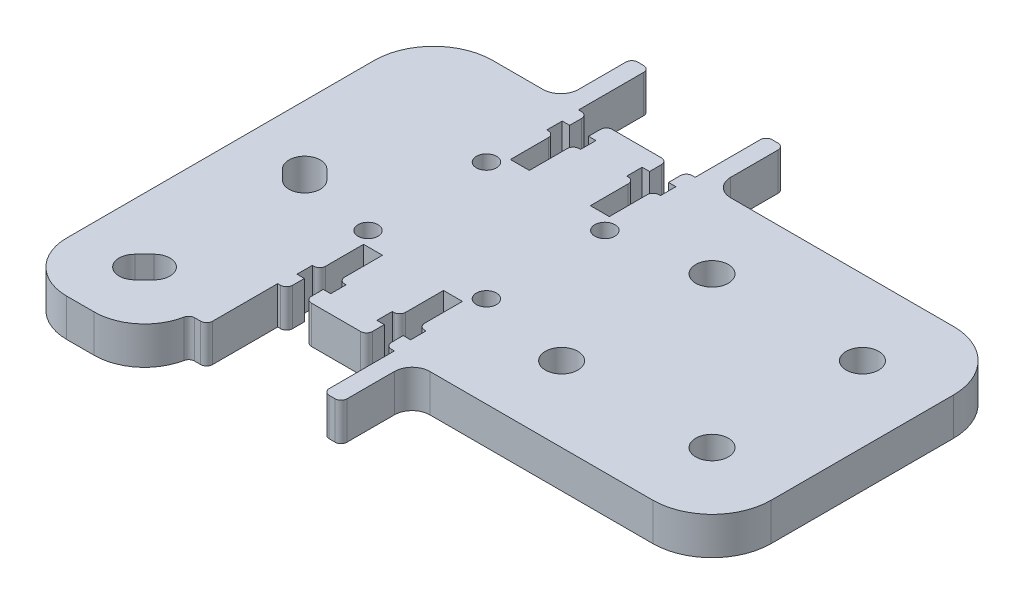
SolidWorks part; units mm, degrees
material "6061-T6 (SS)"
ref_plane "Front" through (0, 0, 0) normal (0, 0, 1) x (1, 0, 0)
ref_plane "Top" through (0, 0, 0) normal (0, 1, 0) x (1, 0, 0)
ref_plane "Right" through (0, 0, 0) normal (1, 0, 0) x (0, 0, -1)
sketch "Sketch1" plane through (0, 0, 0) normal (0, 1, 0) x (1, 0, 0)
  line L0 (-12.7, 25.4) -> (-12.7, -25.4) construction
  line L1 (38.1, -25.4) -> (-38.1, -25.4)
  line L2 (38.1, -25.4) -> (38.1, 25.4)
  line L3 (38.1, 25.4) -> (-38.1, 25.4)
  line L4 (-38.1, -25.4) -> (-38.1, 25.4) construction
  line L5 (38.1, -25.4) -> (-38.1, 25.4) construction
  line L6 (38.1, 25.4) -> (-38.1, -25.4) construction
  line L7 (25.4, -25.4) -> (25.4, 25.4) construction
  line L8 (0, 25.4) -> (0, -25.4) construction
  line L9 (38.1, 0) -> (-38.1, 0) construction
  line L10 (-12.7, 0) -> (-38.1, 0) construction
  line L11 (0, 0) -> (0, 25.4) construction
  line L12 (0, 12.7) -> (38.1, 12.7) construction
  line L13 (-25.4, 0) -> (-25.4, 25.4) construction
  line L14 (-15.4, 10) -> (-35.4, 10) construction
  line L15 (-38.1, 25.4) -> (-59.74, 25.4)
  line L16 (-59.74, 25.4) -> (-59.74, -45.04)
  line L17 (-59.74, -45.04) -> (-38.1, -45.04)
  line L18 (-38.1, -45.04) -> (-38.1, -25.4)
  line L19 (-38.1, 0) -> (-49.74, 0) construction
  line L20 (-49.74, -41.4) -> (-2.5231, -41.4) construction
  line L21 (-49.74, -35.04) -> (-49.74, -45.04) construction
  line L22 (-49.74, -6.36) -> (-49.74, -35.04) construction
  line L23 (-49.74, -6.36) -> (-59.74, -6.36) construction
  line L24 (-49.74, -6.36) -> (-49.74, -8.86) construction
  line L25 (-56.1, -6.36) -> (-56.1, -8) construction
  line L26 (-49.74, -6.36) -> (-48.1, -8) construction
  line L27 (-56.1, -6.36) -> (-56.1, -35.04) construction
  line L28 (-49.74, -35.04) -> (-48.1, -33.4) construction
  line L29 (-15.4, 12.5) -> (-35.4, 12.5) construction
  line L30 (-35.4, 12.5) -> (-35.4, 10) construction
  circle A0 centre (-15.4, 10) radius 1.5 construction
  circle A1 centre (-35.4, 10) radius 1.5 construction
  circle A2 centre (-35.4, -10) radius 1.5 construction
  circle A3 centre (-15.4, -10) radius 1.5 construction
  circle A4 centre (0, 12.7) radius 2.5 construction
  circle A5 centre (25.4, 12.7) radius 2.5 construction
  circle A6 centre (25.4, -12.7) radius 2.5 construction
  circle A7 centre (0, -12.7) radius 2.5 construction
  circle A8 centre (-49.74, -6.36) radius 6.36 construction
  circle A9 centre (-49.74, -35.04) radius 6.36 construction
  circle A10 centre (-49.74, -6.36) radius 10 construction
  circle A11 centre (-49.74, -35.04) radius 10 construction
  circle A12 centre (-49.74, -6.36) radius 2.5 construction
  circle A13 centre (-49.74, -35.04) radius 2.5 construction
  circle A14 centre (-48.1, -8) radius 8 construction
  circle A15 centre (-48.1, -8) radius 10 construction
  circle A16 centre (-48.1, -33.4) radius 8 construction
  point P0 (0, 0)
  point P23 (-25.4, 10)
  point P64 (-25.4, 12.5)
  dimension "D8" = 3
  dimension "D9" = 5
  dimension "D10" = 12.72
  dimension "D11" = 5
  dimension "D12" = 20
  dimension "D14" = 16
  dimension "D15" = 12.5
  dimension "D1" = 50.8
  dimension "D2" = 76.2
  dimension "D3" = 12.7
  dimension "D4" = 25.4
  dimension "D5" = 25.4
  dimension "D6" = 10
  dimension "D7" = 20
  dimension "D13" = 16
extrude "Boss-Extrude1" add sketch "Sketch1" along normal blind 6.35
fillet "Fillet1" radius 8.5 2 edges at (-59.74, 3.175, 45.04) (-38.1, 3.175, 45.04)
fillet "Fillet2" radius 10 3 edges at (38.1, 3.175, -25.4) (38.1, 3.175, 25.4) (-59.74, 3.175, -25.4)
hole_wizard "M5 Clearance Hole1" positions "Sketch3" profile "Sketch2" hole size "M5" standard "ISO" end condition through all
sketch "Sketch3" plane through (0, 6.35, 0) normal (0, 1, 0) x (-1, 0, 0)
  point P6 (0, 12.7)
  point P9 (-25.4, 12.7)
  point P12 (-25.4, -12.7)
  point P15 (0, -12.7)
sketch "Sketch2" plane through (0, 6.35, 12.7) normal (1, 0, 0) x (0, 0, 1)
  line L0 (0, 0) -> (0, 6.35)
  line L1 (0, 6.35) -> (2.75, 6.35)
  line L2 (2.75, 6.35) -> (2.75, 0)
  line L5 (2.75, 0) -> (0, 0)
  line L11 (0, -6.35) -> (0, 107.95) construction
  dimension "Thru Hole Dia." = 5.5
  dimension "Thru Hole Depth" = 6.35
hole_wizard "M3 Clearance Hole1" positions "Sketch5" profile "Sketch4" hole size "M3" standard "ISO" end condition through all
sketch "Sketch5" plane through (0, 6.35, 0) normal (0, 1, 0) x (-1, 0, 0)
  point P0 (15.4, 10)
  point P3 (15.4, -10)
  point P6 (35.4, -10)
  point P9 (35.4, 10)
sketch "Sketch4" plane through (-15.4, 6.35, 10) normal (1, 0, 0) x (0, 0, 1)
  line L0 (0, 0) -> (0, 6.35)
  line L1 (0, 6.35) -> (1.7, 6.35)
  line L2 (1.7, 6.35) -> (1.7, 0)
  line L5 (1.7, 0) -> (0, 0)
  line L11 (0, -6.35) -> (0, 107.95) construction
  dimension "Thru Hole Dia." = 3.4
  dimension "Thru Hole Depth" = 6.35
sketch "Sketch8" plane through (0, 6.35, 0) normal (0, 1, 0) x (1, 0, 0)
  line L0 (-49.74, -6.36) -> (-48.1, -8) construction
  line L1 (-51.6138, -8.2338) -> (-49.9738, -9.8738)
  line L2 (-47.8662, -4.4862) -> (-46.2262, -6.1262)
  line L3 (-49.74, -35.04) -> (-48.1, -33.4) construction
  line L4 (-47.8662, -36.9138) -> (-46.2262, -35.2738)
  line L5 (-51.6138, -33.1662) -> (-49.9738, -31.5262)
  arc A0 (-51.6138, -8.2338) -> (-47.8662, -4.4862) centre (-49.74, -6.36) cw
  arc A1 (-49.9738, -9.8738) -> (-46.2262, -6.1262) centre (-48.1, -8) ccw
  arc A2 (-47.8662, -36.9138) -> (-51.6138, -33.1662) centre (-49.74, -35.04) cw
  arc A3 (-46.2262, -35.2738) -> (-49.9738, -31.5262) centre (-48.1, -33.4) ccw
  dimension "D1" = 2.65
  dimension "D2" = 2.65
  dimension "D3" = 2.65
  dimension "D4" = 2.65
extrude "Cut-Extrude1" cut sketch "Sketch8" against normal through all
sketch "Sketch9" plane through (0, 6.35, 0) normal (0, 1, 0) x (1, 0, 0)
  line L0 (-25.4, 25.4) -> (-25.4, 0) construction
  line L1 (-15.55, 25.4) -> (-12.55, 25.4)
  line L2 (-15.55, 25.4) -> (-15.55, 37.4)
  line L3 (-15.55, 37.4) -> (-12.55, 37.4)
  line L4 (-12.55, 25.4) -> (-12.55, 37.4)
  line L5 (-38.25, 25.4) -> (-38.25, 37.4)
  line L6 (-35.25, 37.4) -> (-38.25, 37.4)
  line L7 (-35.25, 25.4) -> (-35.25, 37.4)
  line L8 (-35.25, 25.4) -> (-38.25, 25.4)
  line L9 (-38.1, 0) -> (0, 0) construction
  line L10 (38.1, 25.4) -> (-38.1, 25.4) construction
  line L11 (38.1, 0) -> (-38.1, 0) construction
  line L12 (-35.25, -25.4) -> (-38.25, -25.4)
  line L13 (-35.25, -25.4) -> (-35.25, -37.4)
  line L14 (-35.25, -37.4) -> (-38.25, -37.4)
  line L15 (-38.25, -25.4) -> (-38.25, -37.4)
  line L16 (-12.55, -25.4) -> (-12.55, -37.4)
  line L17 (-15.55, -37.4) -> (-12.55, -37.4)
  line L18 (-15.55, -25.4) -> (-15.55, -37.4)
  line L19 (-15.55, -25.4) -> (-12.55, -25.4)
  dimension "D1" = 12
  dimension "D2" = 3
  dimension "D3" = 19.7
extrude "Boss-Extrude2" add sketch "Sketch9" against normal up to surface (6.35 mm away) up to face at (-48.92, 0, 34.22)
sketch "Sketch10" plane through (0, 6.35, 0) normal (0, 1, 0) x (1, 0, 0)
  line L0 (-25.4, 25.4) -> (-25.4, -25.4) construction
  line L1 (-38.1, 0) -> (0, 0) construction
  line L2 (-32.15, 25.4) -> (-32.15, 12.4) construction
  line L3 (-33.75, 12.4) -> (-30.55, 12.4)
  line L4 (-30.55, 12.4) -> (-30.55, 19.8)
  line L5 (-30.55, 19.8) -> (-29.3, 19.8)
  line L6 (-29.3, 19.8) -> (-29.3, 22.4)
  line L7 (-29.3, 22.4) -> (-30.55, 22.4)
  line L8 (-30.55, 22.4) -> (-30.55, 25.4)
  line L9 (-30.55, 25.4) -> (-33.75, 25.4)
  line L10 (-33.75, 22.4) -> (-33.75, 25.4)
  line L11 (-35, 22.4) -> (-33.75, 22.4)
  line L12 (-35, 19.8) -> (-35, 22.4)
  line L13 (-33.75, 19.8) -> (-35, 19.8)
  line L14 (-33.75, 12.4) -> (-33.75, 19.8)
  line L15 (38.1, -25.4) -> (-38.1, -25.4) construction
  line L16 (38.1, 25.4) -> (-38.1, 25.4) construction
  line L17 (-20.25, 12.4) -> (-20.25, 19.8)
  line L18 (-17.05, 12.4) -> (-20.25, 12.4)
  line L19 (-17.05, 12.4) -> (-17.05, 19.8)
  line L20 (-17.05, 19.8) -> (-15.8, 19.8)
  line L21 (-15.8, 19.8) -> (-15.8, 22.4)
  line L22 (-15.8, 22.4) -> (-17.05, 22.4)
  line L23 (-17.05, 22.4) -> (-17.05, 25.4)
  line L24 (-20.25, 25.4) -> (-17.05, 25.4)
  line L25 (-20.25, 22.4) -> (-20.25, 25.4)
  line L26 (-21.5, 22.4) -> (-20.25, 22.4)
  line L27 (-21.5, 19.8) -> (-21.5, 22.4)
  line L28 (-20.25, 19.8) -> (-21.5, 19.8)
  line L29 (-20.25, -22.4) -> (-20.25, -25.4)
  line L30 (-21.5, -22.4) -> (-20.25, -22.4)
  line L31 (-21.5, -19.8) -> (-21.5, -22.4)
  line L32 (-20.25, -19.8) -> (-21.5, -19.8)
  line L33 (-20.25, -12.4) -> (-20.25, -19.8)
  line L34 (-17.05, -12.4) -> (-20.25, -12.4)
  line L35 (-17.05, -12.4) -> (-17.05, -19.8)
  line L36 (-17.05, -19.8) -> (-15.8, -19.8)
  line L37 (-15.8, -19.8) -> (-15.8, -22.4)
  line L38 (-15.8, -22.4) -> (-17.05, -22.4)
  line L39 (-17.05, -22.4) -> (-17.05, -25.4)
  line L40 (-20.25, -25.4) -> (-17.05, -25.4)
  line L41 (-30.55, -22.4) -> (-30.55, -25.4)
  line L42 (-29.3, -22.4) -> (-30.55, -22.4)
  line L43 (-29.3, -19.8) -> (-29.3, -22.4)
  line L44 (-30.55, -19.8) -> (-29.3, -19.8)
  line L45 (-30.55, -12.4) -> (-30.55, -19.8)
  line L46 (-33.75, -12.4) -> (-30.55, -12.4)
  line L47 (-33.75, -12.4) -> (-33.75, -19.8)
  line L48 (-33.75, -19.8) -> (-35, -19.8)
  line L49 (-35, -19.8) -> (-35, -22.4)
  line L50 (-35, -22.4) -> (-33.75, -22.4)
  line L51 (-33.75, -22.4) -> (-33.75, -25.4)
  line L52 (-30.55, -25.4) -> (-33.75, -25.4)
  dimension "D1" = 5.7
  dimension "D2" = 2.6
  dimension "D3" = 3.2
  dimension "D4" = 13.5
  dimension "D5" = 13
  dimension "D6" = 3
extrude "Cut-Extrude2" cut sketch "Sketch10" against normal through all
fillet "Fillet3" radius 1 24 edges at (-15.55, 3.175, -37.4) (-12.55, 3.175, -37.4) (-38.25, 3.175, -37.4) (-35.25, 3.175, -37.4) (-38.1436, 3.175, 37.4) (-35.25, 3.175, 37.4) (-12.55, 3.175, 37.4) (-15.55, 3.175, 37.4) (-30.55, 3.175, -19.8) (-33.75, 3.175, -19.8) (-33.75, 3.175, -25.4) (-30.55, 3.175, -25.4) (-20.25, 3.175, -19.8) (-20.25, 3.175, -25.4) (-17.05, 3.175, -25.4) (-17.05, 3.175, -19.8) (-20.25, 3.175, 19.8) (-17.05, 3.175, 19.8) (-17.05, 3.175, 25.4) (-20.25, 3.175, 25.4) (-30.55, 3.175, 25.4) (-33.75, 3.175, 25.4) (-33.75, 3.175, 19.8) (-30.55, 3.175, 19.8)
fillet "Fillet4" radius 3 3 edges at (-38.25, 3.175, -25.4) (-12.55, 3.175, -25.4) (-12.55, 3.175, 25.4)
